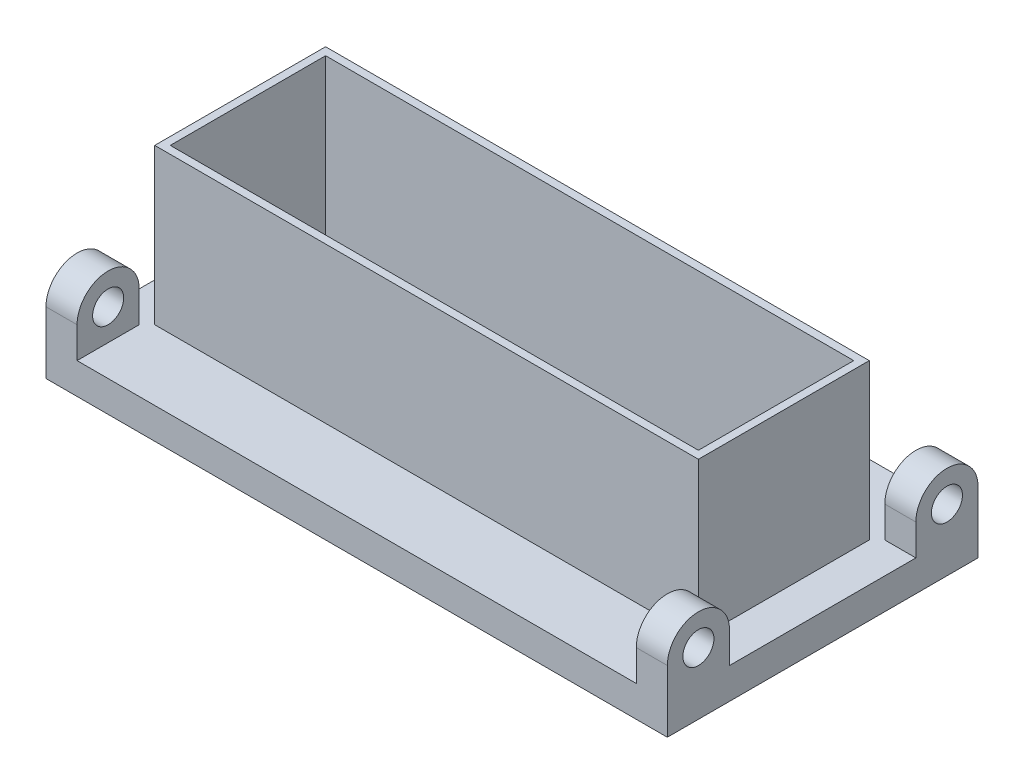
SolidWorks part; units mm, degrees
ref_plane "Front Plane" through (0, 0, 0) normal (0, 0, 1) x (1, 0, 0)
ref_plane "Top Plane" through (0, 0, 0) normal (0, 1, 0) x (1, 0, 0)
ref_plane "Right Plane" through (0, 0, 0) normal (1, 0, 0) x (0, 0, -1)
sketch "Sketch1" plane through (0, 0, 0) normal (1, 0, 0) x (0, 0, -1)
  line L1 (-50, 5) -> (50, 5)
  line L2 (-50, 5) -> (-50, -5)
  line L3 (-50, -5) -> (50, -5)
  line L4 (50, 5) -> (50, -5)
  line L5 (-50, 5) -> (50, -5) construction
  line L6 (-50, -5) -> (50, 5) construction
  point P0 (0, 0)
  dimension "D1" = 100
  dimension "D2" = 10
extrude "Boss-Extrude1" add sketch "Sketch1" along normal mid plane 200
sketch "Sketch2" plane through (100, 0, 0) normal (1, 0, 0) x (0, 0, -1)
  line L0 (-50, 15) -> (-50, 5)
  line L1 (-30, 15) -> (-30, 5)
  line L2 (50, 5) -> (-50, 5) construction
  circle A0 centre (-40, 15) radius 5
  circle A1 centre (-40, 15) radius 10
  line M5 (50, 5) -> (-50, 5)
  dimension "D1" = 10
  dimension "D2" = 20
  dimension "D3" = 10
extrude "Boss-Extrude2" add sketch "Sketch2" against normal blind 10 contours A1 A0 | A1 L0 M5 | A1 L1 M5
mirror "Mirror1" about plane through (0, 0, 0) normal (0, 0, 1) of "Boss-Extrude2"
mirror "Mirror2" about plane through (0, 0, 0) normal (1, 0, 0) of "Mirror1", "Boss-Extrude2"
sketch "Sketch3" plane through (0, 5, 0) normal (0, 1, 0) x (1, 0, 0)
  line L0 (-90, 30) -> (-100, 30) construction
  line L1 (-87.5, 27.5) -> (87.5, 27.5)
  line L2 (-87.5, 27.5) -> (-87.5, -27.5)
  line L3 (-87.5, -27.5) -> (87.5, -27.5)
  line L4 (87.5, 27.5) -> (87.5, -27.5)
  line L5 (-87.5, 27.5) -> (87.5, -27.5) construction
  line L6 (-87.5, -27.5) -> (87.5, 27.5) construction
  line L7 (-85, 25) -> (85, 25)
  line L8 (-85, 25) -> (-85, -25)
  line L9 (-85, -25) -> (85, -25)
  line L10 (85, 25) -> (85, -25)
  line L11 (-85, 25) -> (85, -25) construction
  line L12 (-85, -25) -> (85, 25) construction
  line L13 (-90, -30) -> (-90, -50) construction
  point P0 (0, 0)
  point P7 (0, 0)
  point P12 (0, 0)
  point P13 (0, 0)
  dimension "D1" = 2.5
  dimension "D2" = 2.5
  dimension "D3" = 2.5
  dimension "D4" = 2.5
extrude "Boss-Extrude5" add sketch "Sketch3" along normal blind 50 contours L4 L1 L2 L3 L7 L10 L9 L8
